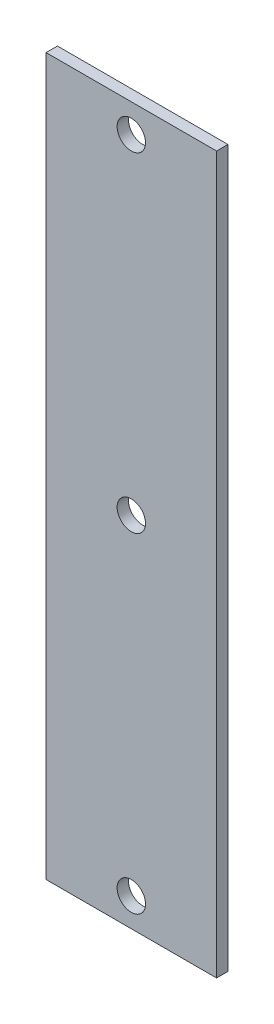
SolidWorks part; units mm, degrees
ref_plane "Front Plane" through (0, 0, 0) normal (0, 0, 1) x (1, 0, 0)
ref_plane "Top Plane" through (0, 0, 0) normal (0, 1, 0) x (1, 0, 0)
ref_plane "Right Plane" through (0, 0, 0) normal (1, 0, 0) x (0, 0, -1)
sketch "Sketch1" plane through (0, 0, 0) normal (0, 0, 1) x (1, 0, 0)
  line L1 (-15, 63) -> (15, 63)
  line L2 (-15, 63) -> (-15, -63)
  line L3 (-15, -63) -> (15, -63)
  line L4 (15, 63) -> (15, -63)
  line L5 (-15, 63) -> (15, -63) construction
  line L6 (-15, -63) -> (15, 63) construction
  circle A0 centre (0, 58) radius 2.5
  circle A1 centre (0, -58) radius 2.5
  circle A2 centre (0, 0) radius 2.5
  point P0 (0, 0)
  dimension "D3" = 5
  dimension "D1" = 30
  dimension "D2" = 126
  dimension "D4" = 5
extrude "Boss-Extrude1" add sketch "Sketch1" along normal blind 2
